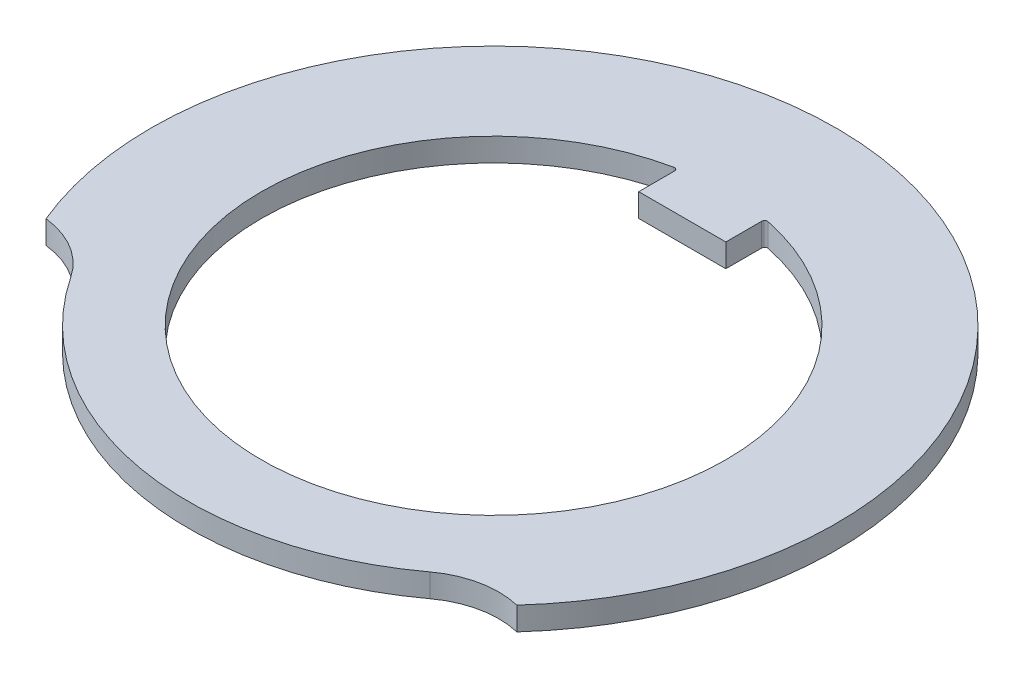
SolidWorks part; units mm, degrees
ref_plane "Front Plane" through (0, 0, 0) normal (0, 0, 1) x (1, 0, 0)
ref_plane "Top Plane" through (0, 0, 0) normal (0, 1, 0) x (1, 0, 0)
ref_plane "Right Plane" through (0, 0, 0) normal (1, 0, 0) x (0, 0, -1)
sketch "Sketch1" plane through (0, 0, 0) normal (0, 1, 0) x (1, 0, 0)
  line L0 (0, 11.8) -> (0, -10.5) construction
  line L2 (0, 0) -> (-10.9018, -4.5157) construction
  line L3 (0, 0) -> (8.7346, -7.9339) construction
  line L5 (0, 0) -> (11.8, 0) construction
  line L6 (-1.5, 6.5) -> (1.5, 6.5)
  line L7 (-1.5, 6.5) -> (-1.5, 7.8581)
  line L9 (1.5, 6.5) -> (1.5, 7.8581)
  line L10 (-1.5, 6.5) -> (0, 8) construction
  line L11 (0, 8) -> (1.5, 6.5) construction
  arc A0 (8.7346, -7.9339) -> (-10.9018, -4.5157) centre (0, 0) ccw
  arc A1 (-1.5, 7.8581) -> (1.5, 7.8581) centre (0, 0) ccw
  arc A2 (-8.7315, -5.8318) -> (6.2472, -8.4393) centre (0, 0) ccw
  arc A3 (6.2472, -8.4393) -> (8.7346, -7.9339) centre (8.0322, -10.8505) cw
  arc A4 (-10.9018, -4.5157) -> (-8.7315, -5.8318) centre (-11.2263, -7.4981) cw
  point P4 (0, 8)
  dimension "D1" = 23.6
  dimension "D2" = 16
  dimension "D3" = 10.5
  dimension "D6" = 3
  dimension "D7" = 3
  dimension "D4" = 132.25
  dimension "D5" = 115.25
  dimension "D10" = 6.5
  dimension "D11" = 3
extrude "Boss-Extrude1" add sketch "Sketch1" along normal blind 0.8
fillet "Fillet1" radius 0.1 2 edges at (-1.5, 0.4, -7.8581) (1.5, 0.4, -7.8581)
